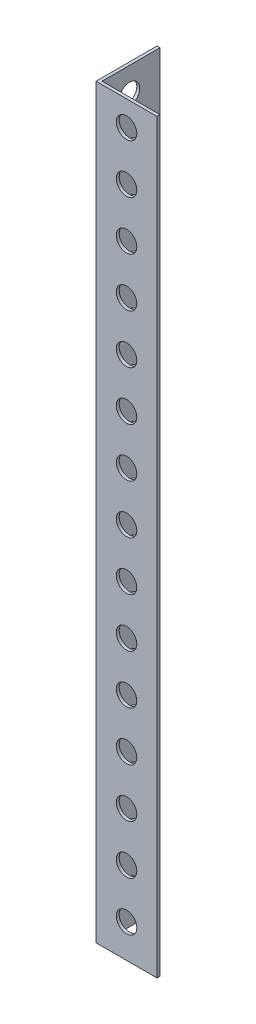
SolidWorks part; units mm, degrees
ref_plane "Front Plane" through (0, 0, 0) normal (0, 0, 1) x (1, 0, 0)
ref_plane "Top Plane" through (0, 0, 0) normal (0, 1, 0) x (1, 0, 0)
ref_plane "Right Plane" through (0, 0, 0) normal (1, 0, 0) x (0, 0, -1)
sketch "Sketch1" plane through (0, 0, 0) normal (0, 1, 0) x (1, 0, 0)
  line L0 (0, 0) -> (31.75, 0)
  line L1 (31.75, 0) -> (31.75, 1.54)
  line L2 (31.75, 1.54) -> (1.54, 1.54)
  line L3 (1.54, 1.54) -> (1.54, 31.75)
  line L4 (1.54, 31.75) -> (0, 31.75)
  line L5 (0, 31.75) -> (0, 0)
  dimension "D1" = 31.75
  dimension "D2" = 31.75
  dimension "D3" = 1.54
  dimension "D4" = 1.54
extrude "Boss-Extrude2" add sketch "Sketch1" along normal blind 388.752
sketch "Sketch2" plane through (0, 0, 0) normal (-1, 0, 0) x (0, 0, 1)
  line L0 (-15.875, 388.752) -> (-15.875, 375.752) construction
  line L1 (-31.75, 388.752) -> (0, 388.752) construction
  circle A0 centre (-15.875, 375.752) radius 5.35
  dimension "D2" = 10.7
  dimension "D1" = 13
extrude "Cut-Extrude1" cut sketch "Sketch2" against normal through all
sketch "Sketch3" plane through (0, 0, 0) normal (0, 0, 1) x (1, 0, 0)
  line L0 (15.875, 388.752) -> (15.875, 375.752) construction
  line L1 (0, 388.752) -> (31.75, 388.752) construction
  circle A0 centre (15.875, 375.752) radius 5.35
  dimension "D2" = 10.7
  dimension "D1" = 13
extrude "Cut-Extrude2" cut sketch "Sketch3" against normal through all
pattern_linear "LPattern2" count 15 spacing 25.6 along (0, -1, 0) of "Cut-Extrude1", "Cut-Extrude2"
